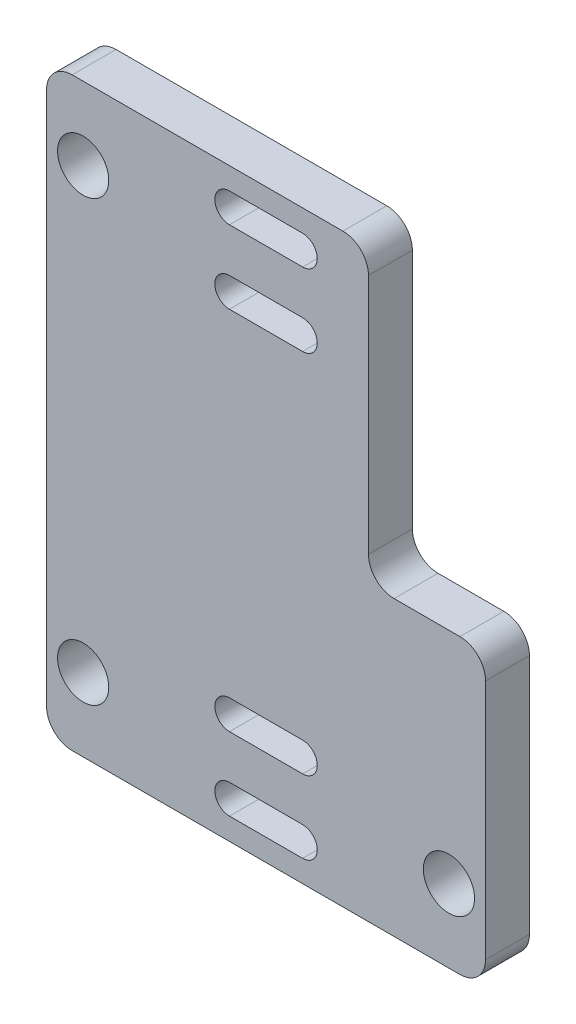
SolidWorks part; units mm, degrees
ref_plane "Plan de face" through (0, 0, 0) normal (0, 0, 1) x (1, 0, 0)
ref_plane "Plan de dessus" through (0, 0, 0) normal (0, 1, 0) x (1, 0, 0)
ref_plane "Plan de droite" through (0, 0, 0) normal (1, 0, 0) x (0, 0, -1)
sketch "Esquisse1" plane through (0, 0, 0) normal (0, 0, 1) x (1, 0, 0)
  line L0 (0, 0) -> (-12.5, 0) construction
  line L1 (-2.5, -12.5) -> (2.5, -12.5) construction
  line L4 (-2.5, -11.5) -> (2.5, -11.5)
  line L6 (-12.5, 15) -> (12.5, 15) construction
  line L7 (-12.5, 15) -> (-12.5, -15) construction
  line L8 (-12.5, -15) -> (12.5, -15) construction
  line L9 (12.5, 15) -> (12.5, -15) construction
  line L10 (-15, 20) -> (15, 20) construction
  line L11 (-15, 20) -> (-15, -20)
  line L12 (-15, -20) -> (15, -20)
  line L13 (15, 20) -> (15, -20) construction
  line L14 (-2.5, -13.5) -> (2.5, -13.5)
  line L15 (0, -20) -> (0, -15) construction
  line L16 (-2.5, -17.5) -> (2.5, -17.5) construction
  line L17 (-2.5, -18.5) -> (2.5, -18.5)
  line L18 (-2.5, -16.5) -> (2.5, -16.5)
  line L19 (-2.5, 17.5) -> (2.5, 17.5) construction
  line L20 (-2.5, 18.5) -> (2.5, 18.5)
  line L21 (-2.5, 16.5) -> (2.5, 16.5)
  line L22 (-2.5, 12.5) -> (2.5, 12.5) construction
  line L23 (-2.5, 11.5) -> (2.5, 11.5)
  line L24 (-2.5, 13.5) -> (2.5, 13.5)
  line L25 (7, 20) -> (7, 0)
  line L26 (12.5, 18.4641) -> (9.5, 16.7321) construction
  line L27 (9.5, 16.7321) -> (9.5, 13.2679) construction
  line L28 (9.5, 13.2679) -> (12.5, 11.5359) construction
  line L29 (12.5, 11.5359) -> (15.5, 13.2679) construction
  line L30 (15.5, 13.2679) -> (15.5, 16.7321) construction
  line L31 (15.5, 16.7321) -> (12.5, 18.4641) construction
  line L32 (7, 0) -> (15, 0)
  line L33 (-15, 20) -> (7, 20)
  line L34 (15, -20) -> (15, 0)
  circle A4 centre (-12.5, 15) radius 1.75
  circle A5 centre (12.5, 15) radius 1.75 construction
  circle A6 centre (-12.5, -15) radius 1.75
  circle A7 centre (12.5, -15) radius 1.75
  arc A8 (-2.5, -11.5) -> (-2.5, -13.5) centre (-2.5, -12.5) ccw
  arc A9 (2.5, -13.5) -> (2.5, -11.5) centre (2.5, -12.5) ccw
  arc A10 (-2.5, -18.5) -> (-2.5, -16.5) centre (-2.5, -17.5) cw
  arc A11 (2.5, -16.5) -> (2.5, -18.5) centre (2.5, -17.5) cw
  arc A12 (-2.5, 18.5) -> (-2.5, 16.5) centre (-2.5, 17.5) ccw
  arc A13 (2.5, 16.5) -> (2.5, 18.5) centre (2.5, 17.5) ccw
  arc A14 (-2.5, 11.5) -> (-2.5, 13.5) centre (-2.5, 12.5) cw
  arc A15 (2.5, 13.5) -> (2.5, 11.5) centre (2.5, 12.5) cw
  circle A16 centre (12.5, 15) radius 3 construction
  point P0 (0, -15)
  point P9 (0, -12.5)
  point P10 (0, 15)
  point P12 (-12.5, 0)
  point P16 (-3.5, -12.5)
  point P22 (0, 20)
  point P23 (-15, 0)
  point P28 (3.5, -12.5)
  point P32 (0, -17.5)
  point P41 (0, -17.5)
  point P43 (0, 17.5)
  point P50 (0, 12.5)
  dimension "D5" = 3.5
  dimension "D8" = 6
  dimension "D1" = 25
  dimension "D2" = 30
  dimension "D3" = 2
  dimension "D4" = 7
  dimension "D6" = 40
  dimension "D7" = 30
  dimension "D9" = 8
extrude "Boss.-Extru.1" add sketch "Esquisse1" along normal blind 3 contours L12 L34 L32 L25 L33 L11 A13 L21 A12 L20 A9 L14 A8 L4 A7 A6 A4 L18 A11 L17 A10 L24 A15 L23 A14
fillet "Congé1" radius 1.75 6 edges at (-15, 20, 1.5) (7, 20, 1.5) (7, 0, 1.5) (15, 0, 1.5) (-15, -20, 1.5) (15, -20, 1.5)
